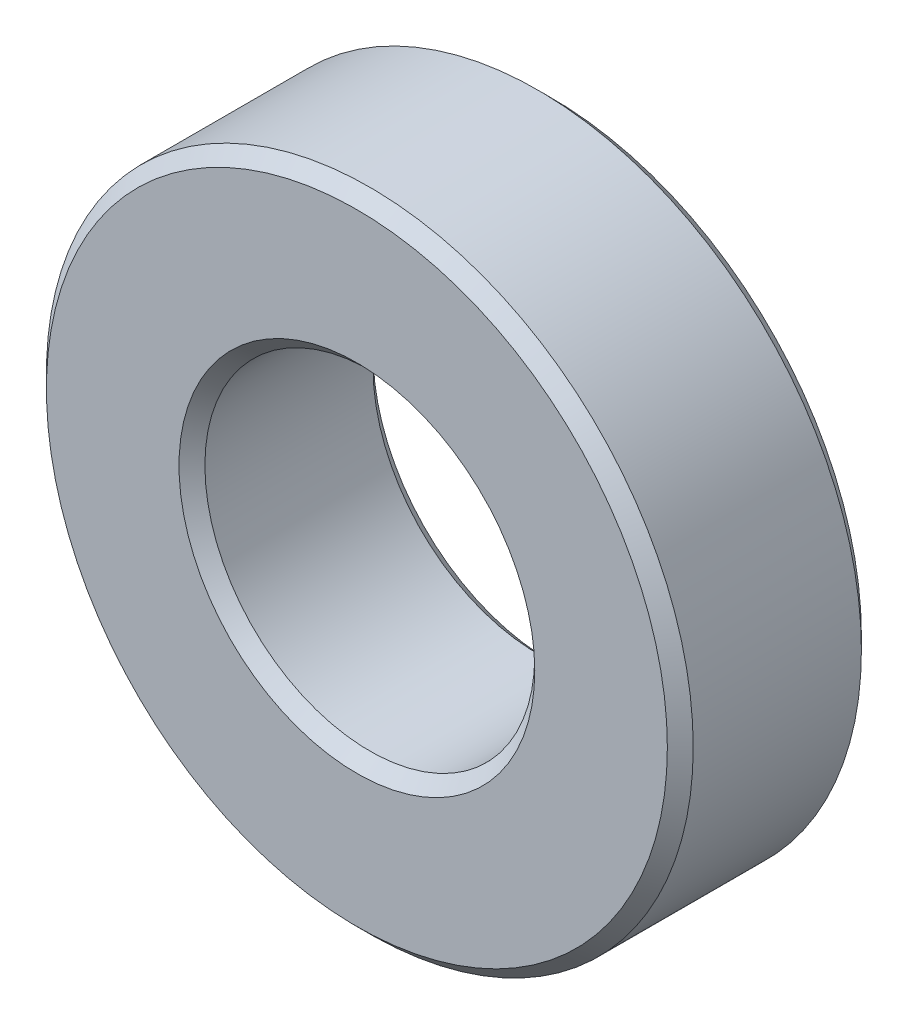
SolidWorks part; units mm, degrees
material "6061-T6 (SS)"
ref_plane "Front Plane" through (0, 0, 0) normal (0, 0, 1) x (1, 0, 0)
ref_plane "Top Plane" through (0, 0, 0) normal (0, 1, 0) x (1, 0, 0)
ref_plane "Right Plane" through (0, 0, 0) normal (1, 0, 0) x (0, 0, -1)
sketch "Sketch1" plane through (0, 0, 0) normal (0, 0, 1) x (1, 0, 0)
  circle A0 centre (0, 0) radius 2.55
  circle A1 centre (0, 0) radius 5
  dimension "D1" = 5.1
  dimension "D2" = 10
extrude "Boss-Extrude1" add sketch "Sketch1" along normal blind 3
chamfer "Chamfer1" distance 0.2 angle 45 4 edges at (5, 0, 0) (2.55, 0, 0) (2.55, 0, 3) (5, 0, 3)
